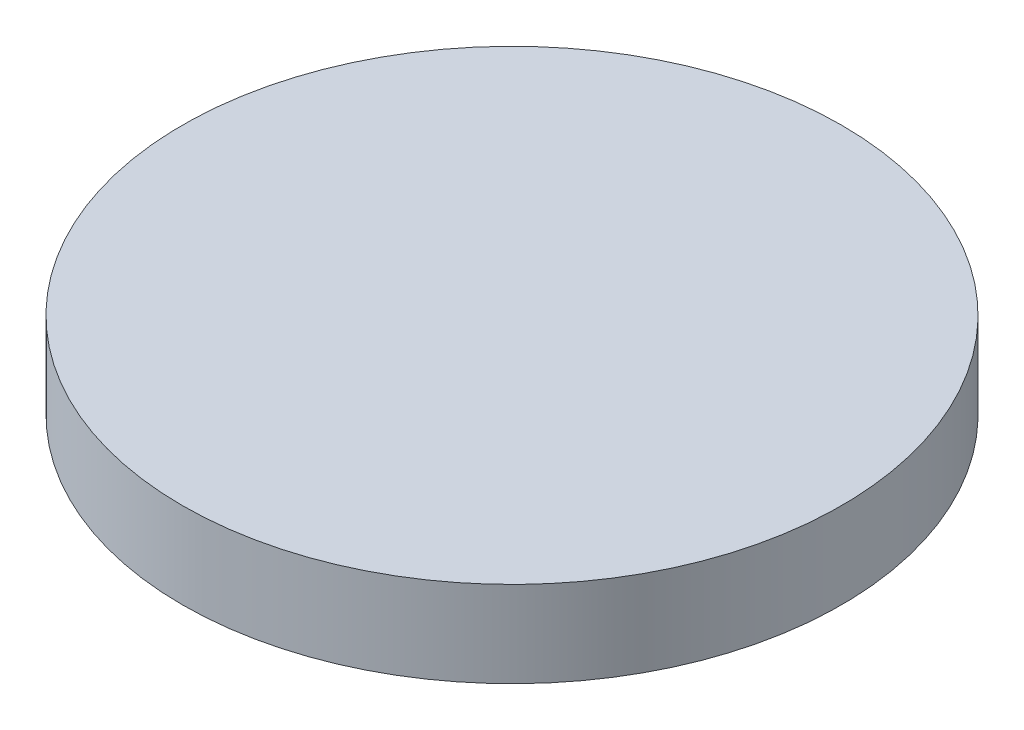
SolidWorks part; units mm, degrees
material "6061 Alloy"
ref_plane "Front Plane" through (0, 0, 0) normal (0, 0, 1) x (1, 0, 0)
ref_plane "Top Plane" through (0, 0, 0) normal (0, 1, 0) x (1, 0, 0)
ref_plane "Right Plane" through (0, 0, 0) normal (1, 0, 0) x (0, 0, -1)
sketch "Sketch1" plane through (0, 0, 0) normal (0, 1, 0) x (1, 0, 0)
  circle A0 centre (0, 0) radius 11.5
  dimension "D1" = 23
extrude "Boss-Extrude1" add sketch "Sketch1" along normal blind 3
